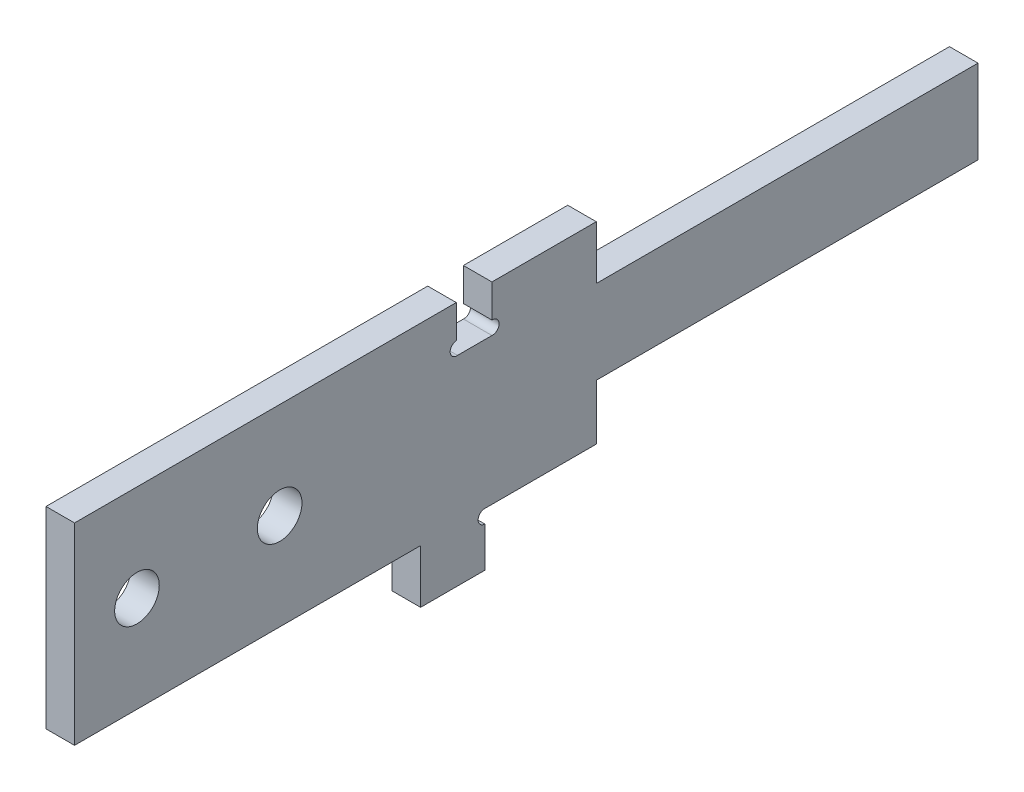
SolidWorks part; units mm, degrees
material "Mosiądz"
ref_plane "Płaszczyzna przednia" through (0, 0, 0) normal (0, 0, 1) x (1, 0, 0)
ref_plane "Płaszczyzna górna" through (0, 0, 0) normal (0, 1, 0) x (1, 0, 0)
ref_plane "Płaszczyzna prawa" through (0, 0, 0) normal (1, 0, 0) x (0, 0, -1)
sketch "Szkic1" plane through (0, 0, 0) normal (0, 0, 1) x (1, 0, 0)
  line L1 (-23.0169, 15.3877) -> (-21.4169, 15.3877)
  line L2 (-23.0169, 15.3877) -> (-23.0169, 4.5877)
  line L3 (-23.0169, 4.5877) -> (-21.4169, 4.5877)
  line L4 (-21.4169, 15.3877) -> (-21.4169, 4.5877)
  dimension "D1" = 1.6
extrude "Dodanie-wyciągnięcie1" add sketch "Szkic1" along normal blind 60
sketch "Szkic2" plane through (-21.4169, 0, 0) normal (1, 0, 0) x (0, 0, -1)
  circle A0 centre (-56.5, 9.9877) radius 1.25
  circle A1 centre (-48.5, 9.9877) radius 1.25
extrude "Wytnij-wyciągnięcie1" cut sketch "Szkic2" against normal blind 60
sketch "Szkic3" plane through (0, 15.3877, 0) normal (0, 1, 0) x (1, 0, 0)
  line L1 (-21.4169, -60) -> (-21.4169, 0) construction
  line L2 (-23.0169, -60) -> (-23.0169, 0) construction
  line L3 (-21.4169, -38.6) -> (-23.0169, -38.6)
  line L4 (-21.4169, -38.6) -> (-21.4169, -36.6)
  line L5 (-21.4169, -36.6) -> (-23.0169, -36.6)
  line L6 (-23.0169, -38.6) -> (-23.0169, -36.6)
  line L7 (-21.4169, -60) -> (-23.0169, -60) construction
  point P10 (-22.2169, -38.6)
  dimension "D1" = 23.4
  dimension "D2" = 2
extrude "Wytnij-wyciągnięcie2" cut sketch "Szkic3" against normal blind 2.6
sketch "Szkic4" plane through (0, 4.5877, 0) normal (0, -1, 0) x (1, 0, 0)
  line L0 (-23.0169, 60) -> (-21.4169, 60) construction
  line L1 (-23.0169, 60) -> (-23.0169, 0) construction
  line L2 (-21.4169, 60) -> (-21.4169, 0) construction
  line L3 (-23.0169, 40.6) -> (-21.4169, 40.6)
  line L4 (-23.0169, 40.6) -> (-23.0169, 38.6)
  line L5 (-23.0169, 38.6) -> (-21.4169, 38.6)
  line L6 (-21.4169, 40.6) -> (-21.4169, 38.6)
  dimension "D1" = 21.4
  dimension "D2" = 2
extrude "Dodanie-wyciągnięcie2" add sketch "Szkic4" along normal blind 3
sketch "Szkic5" plane through (0, 0, 38.6) normal (0, 0, -1) x (-1, 0, 0)
  line L1 (21.4169, 15.3877) -> (23.0169, 15.3877)
  line L2 (21.4169, 15.3877) -> (21.4169, 16.3577)
  line L3 (21.4169, 16.3577) -> (23.0169, 16.3577)
  line L4 (23.0169, 15.3877) -> (23.0169, 16.3577)
sketch "Szkic6" plane through (0, 0, 0) normal (0, 0, -1) x (-1, 0, 0)
  line L1 (21.4169, 4.5877) -> (21.4169, 15.3877) construction
  line L2 (23.0169, 15.3877) -> (23.0169, 4.5877) construction
  line L7 (21.4169, 12.3877) -> (23.0169, 12.3877)
  line L8 (21.4169, 12.3877) -> (21.4169, 15.3877)
  line L9 (21.4169, 15.3877) -> (23.0169, 15.3877)
  line L10 (23.0169, 12.3877) -> (23.0169, 15.3877)
  line L11 (21.4169, 4.5877) -> (23.0169, 4.5877)
  line L12 (21.4169, 4.5877) -> (21.4169, 7.6877)
  line L13 (21.4169, 7.6877) -> (23.0169, 7.6877)
  line L14 (23.0169, 4.5877) -> (23.0169, 7.6877)
extrude "Wytnij-wyciągnięcie3" cut sketch "Szkic6" against normal up to surface (30.75 mm away)
sketch "Szkic7" plane through (0, 0, 0) normal (0, 0, -1) x (-1, 0, 0)
  line L1 (21.4169, 12.3877) -> (23.0169, 12.3877)
  line L2 (21.4169, 12.3877) -> (21.4169, 7.6877)
  line L3 (21.4169, 7.6877) -> (23.0169, 7.6877)
  line L4 (23.0169, 12.3877) -> (23.0169, 7.6877)
extrude "Wytnij-wyciągnięcie4" cut sketch "Szkic7" against normal blind 9.35
sketch "Szkic8" plane through (0, 4.5877, 0) normal (0, -1, 0) x (1, 0, 0)
  line L0 (-21.4169, 38.6) -> (-21.4169, 30.75) construction
  line L1 (-23.0169, 38.6) -> (-21.4169, 38.6)
  line L2 (-23.0169, 38.6) -> (-23.0169, 37)
  line L3 (-23.0169, 37) -> (-21.4169, 37)
  line L4 (-21.4169, 38.6) -> (-21.4169, 37)
  dimension "D1" = 1.6
extrude "Dodanie-wyciągnięcie3" add sketch "Szkic8" along normal up to surface (3 mm away) up to face at (-22.2169, 1.5877, 39.6)
sketch "Szkic9" plane through (-23.0169, 0, 0) normal (-1, 0, 0) x (0, 0, 1)
  line L0 (37, 4.2127) -> (45.317, 4.2127) construction
  line L1 (37, 1.5877) -> (37, 4.5877) construction
  line L2 (37, 4.5877) -> (30.75, 4.5877) construction
  line L3 (44.1353, 13.1627) -> (31.346, 13.1627) construction
  line L4 (36.6, 12.7877) -> (38.6, 12.7877) construction
  circle A0 centre (37, 4.2127) radius 0.375
  circle A1 centre (38.5658, 13.1627) radius 0.3766
  circle A2 centre (36.5735, 13.1627) radius 0.3759
  dimension "D1" = 0.375
  dimension "D2" = 0.375
extrude "Wytnij-wyciągnięcie5" cut sketch "Szkic9" against normal up to surface (1.6 mm away) up to face at (-21.4169, 9.3002, 35.4562)
